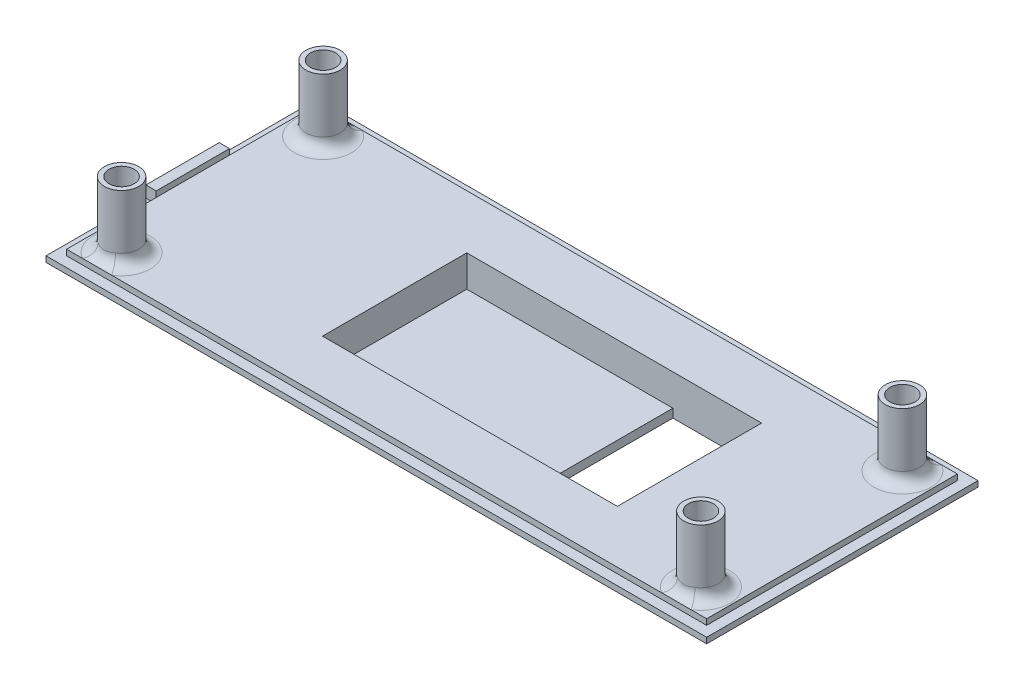
SolidWorks part; units mm, degrees
ref_plane "前视基准面" through (0, 0, 0) normal (0, 0, 1) x (1, 0, 0)
ref_plane "上视基准面" through (0, 0, 0) normal (0, 1, 0) x (1, 0, 0)
ref_plane "右视基准面" through (0, 0, 0) normal (1, 0, 0) x (0, 0, -1)
sketch "草图1" plane through (0, 0, 0) normal (0, 1, 0) x (1, 0, 0)
  line L1 (-57.7, 23.7) -> (57.7, 23.7)
  line L2 (-57.7, 23.7) -> (-57.7, -23.7)
  line L3 (-57.7, -23.7) -> (57.7, -23.7)
  line L4 (57.7, 23.7) -> (57.7, -23.7)
  line L5 (-57.7, 23.7) -> (57.7, -23.7) construction
  line L6 (-57.7, -23.7) -> (57.7, 23.7) construction
  point P0 (0, 0)
  dimension "D1" = 115.4
  dimension "D2" = 47.4
extrude "凸台-拉伸1" add sketch "草图1" along normal blind 1
sketch "草图3" plane through (0, 1, 0) normal (0, 1, 0) x (1, 0, 0)
  line L8 (55.9, -21.9) -> (55.9, 21.9)
  line L9 (55.9, 21.9) -> (-55.9, 21.9)
  line L10 (-55.9, 21.9) -> (-55.9, -21.9)
  line L11 (-55.9, -21.9) -> (55.9, -21.9)
  line L12 (55.9, -21.9) -> (55.9, 21.9)
  line L13 (55.9, 21.9) -> (-55.9, 21.9)
  line L14 (-55.9, 21.9) -> (-55.9, -21.9)
  line L15 (-55.9, -21.9) -> (55.9, -21.9)
  dimension "D1" = 1.8
extrude "凸台-拉伸3" add sketch "草图3" along normal blind 1 contours L12 L13 L14 L15
sketch "草图10" plane through (0, 2, 0) normal (0, 1, 0) x (1, 0, 0)
  line L0 (-55.9, 21.9) -> (-55.9, -21.9) construction
  line L1 (-55.9, 21.9) -> (-55.9, -21.9) construction
  line L2 (55.9, 21.9) -> (-55.9, 21.9) construction
  line L3 (-55.9, -21.9) -> (55.9, -21.9) construction
  line L4 (55.9, -21.9) -> (55.9, 21.9) construction
  circle A0 centre (-50.6, 17.6) radius 3
  circle A1 centre (50.6, 17.6) radius 3
  circle A2 centre (-50.6, -17.6) radius 3
  circle A3 centre (50.6, -17.6) radius 3
  dimension "D1" = 5.3
  dimension "D2" = 5.3
  dimension "D3" = 4.3
  dimension "D4" = 4.3
  dimension "D5" = 5.3
  dimension "D6" = 5.3
  dimension "D7" = 4.3
  dimension "D8" = 4.3
extrude "凸台-拉伸6" add sketch "草图10" along normal blind 11.5
sketch "草图11" plane through (0, 13.5, 0) normal (0, 1, 0) x (1, 0, 0)
  circle A0 centre (-50.6, 17.6) radius 1.5
  circle A1 centre (-50.6, -17.6) radius 1.5
  circle A2 centre (50.6, 17.6) radius 1.5
  circle A3 centre (50.6, -17.6) radius 1.5
extrude "切除-拉伸4" cut sketch "草图11" against normal up to next
sketch "草图12" plane through (0, 13.5, 0) normal (0, 1, 0) x (1, 0, 0)
  circle A0 centre (-50.6, 17.6) radius 2.2
  circle A1 centre (-50.6, -17.6) radius 2.2
  circle A2 centre (50.6, 17.6) radius 2.2
  circle A3 centre (50.6, -17.6) radius 2.2
extrude "切除-拉伸5" cut sketch "草图12" against normal blind 3.5
fillet "圆角1" radius 2 1 edges at (-50.6, 2, -14.6)
fillet "圆角2" radius 2 1 edges at (-50.6, 2, 20.6)
fillet "圆角3" radius 2 1 edges at (50.6, 2, 20.6)
fillet "圆角4" radius 2 1 edges at (50.6, 2, -14.6)
sketch "草图13" plane through (0, 0, 0) normal (0, -1, 0) x (1, 0, 0)
  line L1 (53.8288, -17.4321) -> (52.069, -14.7198)
  line L2 (52.069, -14.7198) -> (48.8402, -14.8877)
  line L3 (48.8402, -14.8877) -> (47.3712, -17.7679)
  line L4 (47.3712, -17.7679) -> (49.131, -20.4802)
  line L5 (49.131, -20.4802) -> (52.3598, -20.3123)
  line L6 (52.3598, -20.3123) -> (53.8288, -17.4321)
  line L7 (53.8297, 17.4494) -> (52.3453, 20.3217)
  line L8 (52.3453, 20.3217) -> (49.1156, 20.4723)
  line L9 (49.1156, 20.4723) -> (47.3703, 17.7506)
  line L10 (47.3703, 17.7506) -> (48.8547, 14.8783)
  line L11 (48.8547, 14.8783) -> (52.0844, 14.7277)
  line L12 (52.0844, 14.7277) -> (53.8297, 17.4494)
  line L13 (-47.3747, -17.3749) -> (-49.1823, -14.6943)
  line L14 (-49.1823, -14.6943) -> (-52.4076, -14.9193)
  line L15 (-52.4076, -14.9193) -> (-53.8253, -17.8251)
  line L16 (-53.8253, -17.8251) -> (-52.0177, -20.5057)
  line L17 (-52.0177, -20.5057) -> (-48.7924, -20.2807)
  line L18 (-48.7924, -20.2807) -> (-47.3747, -17.3749)
  line L19 (-47.3739, 17.3861) -> (-48.8017, 20.2869)
  line L20 (-48.8017, 20.2869) -> (-52.0278, 20.5008)
  line L21 (-52.0278, 20.5008) -> (-53.8261, 17.8139)
  line L22 (-53.8261, 17.8139) -> (-52.3983, 14.9131)
  line L23 (-52.3983, 14.9131) -> (-49.1722, 14.6992)
  line L24 (-49.1722, 14.6992) -> (-47.3739, 17.3861)
  circle A0 centre (50.6, -17.6) radius 2.8 construction
  circle A1 centre (50.6, 17.6) radius 2.8 construction
  circle A2 centre (-50.6, -17.6) radius 2.8 construction
  circle A3 centre (-50.6, 17.6) radius 2.8 construction
extrude "切除-拉伸6" cut sketch "草图13" against normal blind 2
sketch "草图15" plane through (0, 1, 0) normal (0, 1, 0) x (1, 0, 0)
  line L0 (-55.9, 21.9) -> (-55.9, -21.9) construction
  line L1 (-55.9, -6.25) -> (-57.7, -6.25)
  line L2 (-55.9, -6.25) -> (-55.9, 6.55)
  line L3 (-55.9, 6.55) -> (-57.7, 6.55)
  line L4 (-57.7, -6.25) -> (-57.7, 6.55)
  line L5 (-57.7, 23.7) -> (-57.7, -23.7) construction
  dimension "D1" = 17.45
  dimension "D2" = 17.15
extrude "凸台-拉伸8" add sketch "草图15" along normal blind 2
sketch "草图16" plane through (0, 0, 0) normal (0, -1, 0) x (1, 0, 0)
  line L0 (-57.7, -23.7) -> (-57.7, 23.7) construction
  line L1 (-21.8, 14.1) -> (32.7, 14.1)
  line L2 (-21.8, 14.1) -> (-21.8, -14.1)
  line L3 (-21.8, -14.1) -> (32.7, -14.1)
  line L4 (32.7, 14.1) -> (32.7, -14.1)
  line L5 (57.7, 23.7) -> (57.7, -23.7) construction
  point P6 (-21.8, 0)
  point P7 (-57.7, 0)
  dimension "D1" = 28.2
  dimension "D2" = 54.5
  dimension "D3" = 25
  dimension "D4" = 0
extrude "凸台-拉伸9" add sketch "草图16" along normal blind 5
sketch "草图18" plane through (0, 2, 0) normal (0, 1, 0) x (1, 0, 0)
  line L1 (31.1, -12.7) -> (-20.4, -12.7)
  line L2 (31.1, -12.7) -> (31.1, 12.5)
  line L3 (31.1, 12.5) -> (-20.4, 12.5)
  line L4 (-20.4, -12.7) -> (-20.4, 12.5)
  dimension "D1" = 25.2
  dimension "D2" = 51.5
  dimension "D3" = 1.4
  dimension "D4" = 1.4
extrude "切除-拉伸7" cut sketch "草图18" against normal blind 5.5
sketch "草图19" plane through (0, -3.5, 0) normal (0, 1, 0) x (1, 0, 0)
  line L0 (-20.4, -12.7) -> (31.1, -12.7) construction
  line L1 (31.1, 12.5) -> (15.6, 12.5)
  line L2 (31.1, 12.5) -> (31.1, -12.7)
  line L3 (31.1, -12.7) -> (15.6, -12.7)
  line L4 (15.6, 12.5) -> (15.6, -12.7)
  dimension "D1" = 15.5
extrude "切除-拉伸8" cut sketch "草图19" against normal up to next
sketch "草图20" plane through (0, -5, 0) normal (0, -1, 0) x (1, 0, 0)
  line L0 (31.1, 12.7) -> (31.1, -12.5) construction
  line L1 (31.1, -4.9) -> (32.7, -4.9)
  line L2 (31.1, -4.9) -> (31.1, 5.1)
  line L3 (31.1, 5.1) -> (32.7, 5.1)
  line L4 (32.7, -4.9) -> (32.7, 5.1)
  line L5 (32.7, -14.1) -> (32.7, 14.1) construction
  point P8 (31.1, 0.1)
  point P9 (31.1, 0.1)
  dimension "D1" = 10
  dimension "D2" = 0
extrude "切除-拉伸9" cut sketch "草图20" against normal blind 5
fillet "圆角5" radius 2 2 edges at (31.9, 0, 5.1) (31.9, 0, -4.9)
fillet "圆角6" radius 3 5 edges at (-21.8, 0, 0) (5.45, 0, -14.1) (32.7, 0, -8.5) (5.45, 0, 14.1) (32.7, 0, 8.6)
